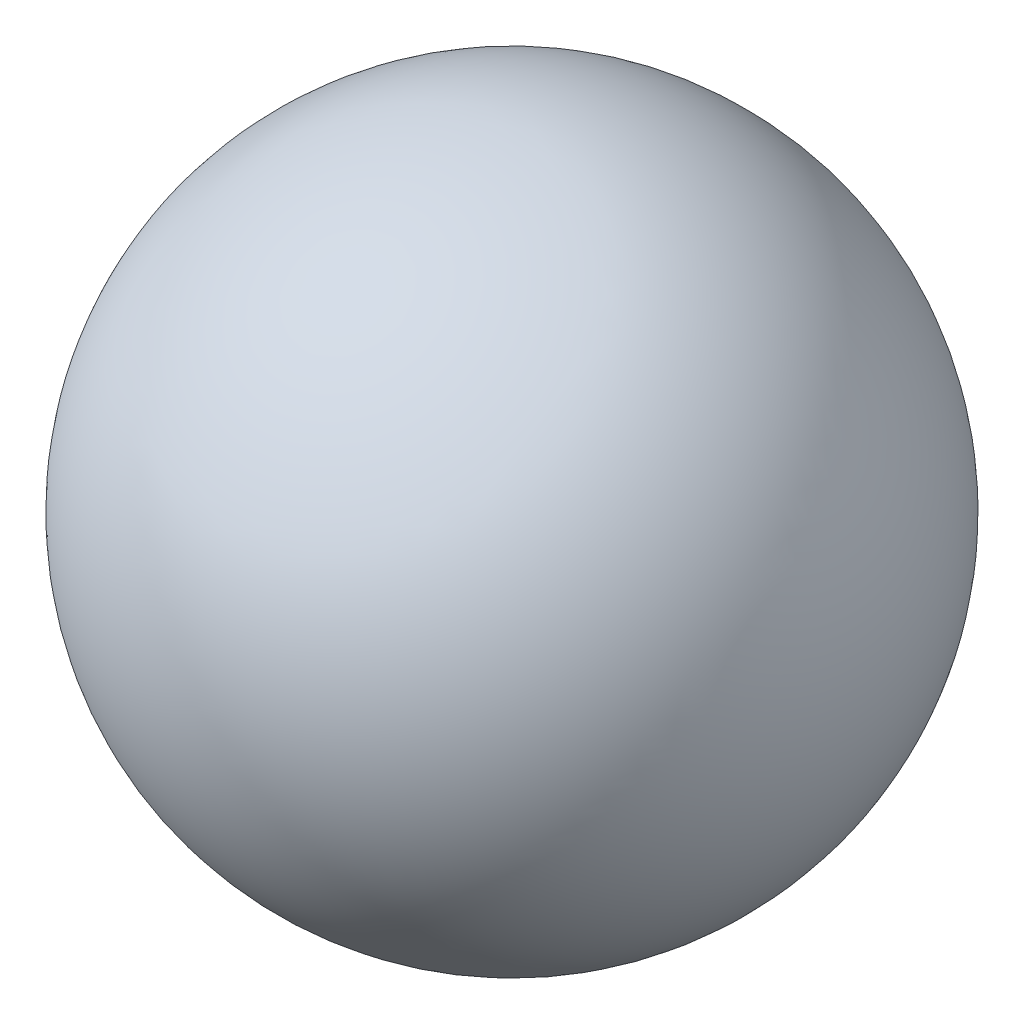
SolidWorks part; units mm, degrees
ref_plane "Front Plane" through (0, 0, 0) normal (0, 0, 1) x (1, 0, 0)
ref_plane "Top Plane" through (0, 0, 0) normal (0, 1, 0) x (1, 0, 0)
ref_plane "Right Plane" through (0, 0, 0) normal (1, 0, 0) x (0, 0, -1)
sketch "Sketch2" plane through (0, 0, 0) normal (0, 0, 1) x (1, 0, 0)
  line L0 (-127, 0) -> (127, 0)
  arc A0 (-127, 0) -> (127, 0) centre (0, 0) cw
  dimension "D1" = 127
revolve "Revolve1" add sketch "Sketch2" angle 360 about L0
